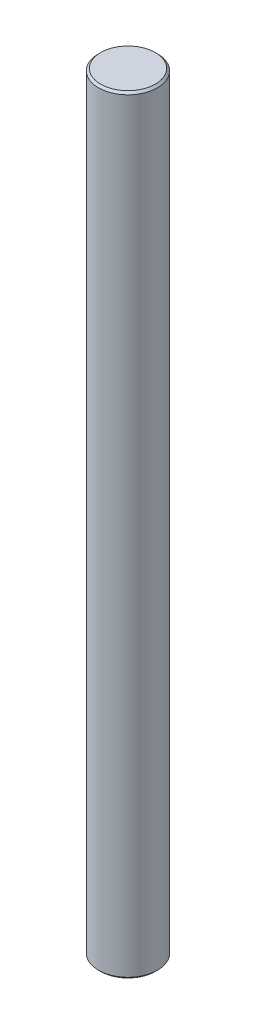
SolidWorks part; units mm, degrees
ref_plane "Front Plane" through (0, 0, 0) normal (0, 0, 1) x (1, 0, 0)
ref_plane "Top Plane" through (0, 0, 0) normal (0, 1, 0) x (1, 0, 0)
ref_plane "Right Plane" through (0, 0, 0) normal (1, 0, 0) x (0, 0, -1)
sketch "Sketch1" plane through (0, 0, 0) normal (0, 1, 0) x (1, 0, 0)
  circle A0 centre (0, 0) radius 14
  dimension "D1" = 28
extrude "Boss-Extrude1" add sketch "Sketch1" along normal mid plane 365
chamfer "Chamfer1" distance 1 angle 45 2 edges at (0, -182.5, 14) (0, 182.5, 14)
